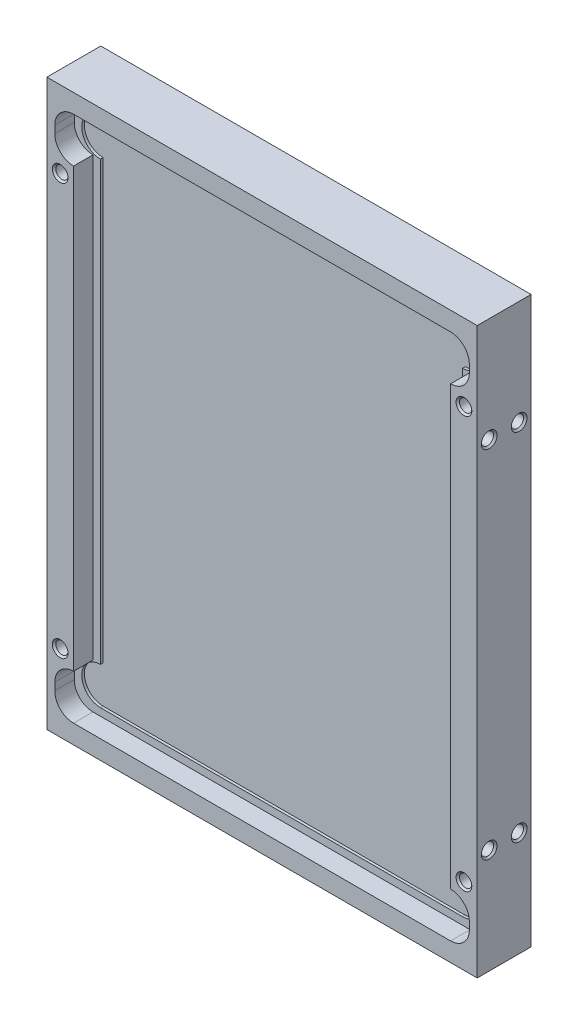
SolidWorks part; units mm, degrees
material "6061-T6 Al"
ref_plane "Front Plane" through (0, 0, 0) normal (0, 0, 1) x (1, 0, 0)
ref_plane "Top Plane" through (0, 0, 0) normal (0, 1, 0) x (1, 0, 0)
ref_plane "Right Plane" through (0, 0, 0) normal (1, 0, 0) x (0, 0, -1)
sketch "Sketch1" plane through (0, 0, 0) normal (0, 0, 1) x (1, 0, 0)
  line L1 (-73.025, 95.885) -> (73.025, 95.885)
  line L2 (-73.025, 95.885) -> (-73.025, -95.885)
  line L3 (-73.025, -95.885) -> (73.025, -95.885)
  line L4 (73.025, 95.885) -> (73.025, -95.885)
  point P4 (-73.025, 0)
  point P6 (0, 95.885)
  dimension "D1" = 191.77
  dimension "D2" = 146.05
extrude "Boss-Extrude1" add sketch "Sketch1" along normal mid plane 18.288
sketch "Sketch4" plane through (0, 0, 9.144) normal (0, 0, 1) x (1, 0, 0)
  line L0 (-63.9953, -74.2569) -> (-63.9953, 74.2569)
  line L1 (-63.9953, 89.4969) -> (63.9953, 89.4969)
  line L2 (63.9953, -74.2569) -> (63.9953, 74.2569)
  line L3 (-63.9953, -89.4969) -> (63.9953, -89.4969)
  line L4 (63.9953, 89.4969) -> (-63.9953, -89.4969) construction
  line L5 (0, 0) -> (-127.9906, 0) construction
  line L6 (0, 0) -> (0, 127.9906) construction
  line L7 (-70.3453, 83.1469) -> (-70.3453, 80.6069)
  line L9 (70.3453, 83.1469) -> (70.3453, 80.6069)
  line L10 (70.3453, -83.1469) -> (70.3453, -80.6069)
  line L11 (-70.3453, -83.1469) -> (-70.3453, -80.6069)
  arc A0 (-63.9953, 89.4969) -> (-70.3453, 83.1469) centre (-63.9953, 83.1469) ccw
  arc A1 (63.9953, 89.4969) -> (70.3453, 83.1469) centre (63.9953, 83.1469) cw
  arc A2 (63.9953, -89.4969) -> (70.3453, -83.1469) centre (63.9953, -83.1469) ccw
  arc A3 (-63.9953, -89.4969) -> (-70.3453, -83.1469) centre (-63.9953, -83.1469) cw
  arc A4 (-70.3453, 80.6069) -> (-63.9953, 74.2569) centre (-63.9953, 80.6069) ccw
  arc A5 (70.3453, 80.6069) -> (63.9953, 74.2569) centre (63.9953, 80.6069) cw
  arc A6 (70.3453, -80.6069) -> (63.9953, -74.2569) centre (63.9953, -80.6069) ccw
  arc A7 (-70.3453, -80.6069) -> (-63.9953, -74.2569) centre (-63.9953, -80.6069) cw
  point P11 (-235.3776, -6.3972)
  point P14 (0, 0)
  dimension "D1" = 6.35
  dimension "D3" = 127.9906
  dimension "D2" = 178.9938
  dimension "D4" = 2.54
extrude "Cut-Extrude1" cut sketch "Sketch4" against normal blind 6.604
sketch "Sketch5" plane through (0, 0, 2.54) normal (0, 0, -1) x (-1, 0, 0)
  line L1 (-61.4553, 86.9569) -> (61.4553, 86.9569)
  line L2 (-61.4553, 74.2569) -> (-61.4553, -74.2569)
  line L3 (-61.4553, -86.9569) -> (61.4553, -86.9569)
  line L4 (61.4553, 74.2569) -> (61.4553, -74.2569)
  line L5 (61.4553, 0) -> (63.9953, 0) construction
  line L6 (-61.4553, -86.9569) -> (61.4553, 86.9569) construction
  line L7 (63.9953, 74.2569) -> (63.9953, -74.2569) construction
  line L9 (61.4553, -86.9569) -> (61.4553, -89.4969) construction
  line L11 (63.9953, 74.2569) -> (63.9953, -74.2569) construction
  line L12 (63.9953, -89.4969) -> (-63.9953, -89.4969) construction
  arc A0 (-61.4553, -74.2569) -> (-61.4553, -86.9569) centre (-61.4553, -80.6069) ccw
  arc A1 (61.4553, -86.9569) -> (61.4553, -74.2569) centre (61.4553, -80.6069) ccw
  arc A2 (61.4553, 86.9569) -> (61.4553, 74.2569) centre (61.4553, 80.6069) cw
  arc A3 (-61.4553, 86.9569) -> (-61.4553, 74.2569) centre (-61.4553, 80.6069) ccw
  arc A4 (70.3453, 83.1469) -> (63.9953, 89.4969) centre (63.9953, 83.1469) ccw construction
  point P0 (0, 0)
  dimension "D2" = 2.54
extrude "Cut-Extrude3" cut sketch "Sketch5" along normal blind 0.889
mirror "Mirror1" about plane through (0, 0, 0) normal (0, 0, 1) of "Cut-Extrude3", "Cut-Extrude1"
hole_wizard "#8-32 Tapped Hole1" positions "3DSketch1" profile "Sketch8" tap size "#8-32" standard "ANSI Inch" end condition through all
sketch3d "3DSketch1"
  line L0 (-68.5165, 69.85, 9.144) -> (0, 0, 9.144) construction
  line L1 (0, 0, 9.144) -> (68.5165, -69.85, 9.144) construction
  point P0 (68.5165, 69.85, 9.144)
  point P3 (-68.5165, 69.85, 9.144)
  point P6 (-68.5165, -69.85, 9.144)
  point P9 (68.5165, -69.85, 9.144)
  dimension "D1" = 137.033
  dimension "D2" = 139.7
sketch "Sketch8" plane through (68.5165, 69.85, 9.144) normal (1, 0, 0) x (0, -1, 0)
  line L0 (0, 0) -> (0, 18.288)
  line L1 (0, 18.288) -> (2.667, 18.288)
  line L2 (2.0828, 17.7038) -> (2.0828, 0.5842)
  line L3 (2.0828, 0.5842) -> (2.667, 0)
  line L5 (2.667, 0) -> (0, 0)
  line L6 (-2.0828, 0.5842) -> (-2.667, 0) construction
  line L7 (2.667, 18.288) -> (2.0828, 17.7038)
  line L8 (-2.667, 18.288) -> (-2.0828, 17.7038) construction
  line L11 (0, -6.35) -> (0, 107.95) construction
  dimension "Thread Major Dia." = 4.1656
  dimension "Thru Tap Drill Depth" = 18.288
  dimension "Near C'Sink Dia." = 5.334
  dimension "Near C'Sink Angle" = 90
  dimension "Far C'Sink Dia." = 5.334
  dimension "Far C'Sink Angle" = 90
hole_wizard "#8-32 Tapped Hole2" positions "Sketch10" profile "Sketch9" tap size "#8-32" standard "ANSI Inch" end condition up to next
sketch "Sketch10" plane through (73.025, 0, 0) normal (1, 0, 0) x (0, 0, -1)
  line L0 (-5.08, 60.325) -> (5.08, -60.325) construction
  line L2 (-2.54, -74.2569) -> (-2.54, 74.2569) construction
  point P7 (5.08, 60.325)
  point P9 (-5.08, -60.325)
  point P11 (5.08, -60.325)
  point P13 (-5.08, 60.325)
  point P20 (-5.54, -58.2836)
  dimension "D1" = 2.54
  dimension "D2" = 120.65
sketch "Sketch9" plane through (73.025, 60.325, -5.08) normal (0, 1, 0) x (0, 0, -1)
  line L0 (0, 0) -> (0, 9.0297)
  line L1 (0, 9.0297) -> (2.0828, 9.0297)
  line L2 (2.0828, 9.0297) -> (2.0828, 0.5842)
  line L3 (2.0828, 0.5842) -> (2.667, 0)
  line L5 (2.667, 0) -> (0, 0)
  line L6 (-2.0828, 0.5842) -> (-2.667, 0) construction
  line L11 (0, -6.35) -> (0, 107.95) construction
  dimension "Thread Major Dia." = 4.1656
  dimension "Thru Tap Drill Depth" = 9.0297
  dimension "Near C'Sink Dia." = 5.334
  dimension "Near C'Sink Angle" = 90
